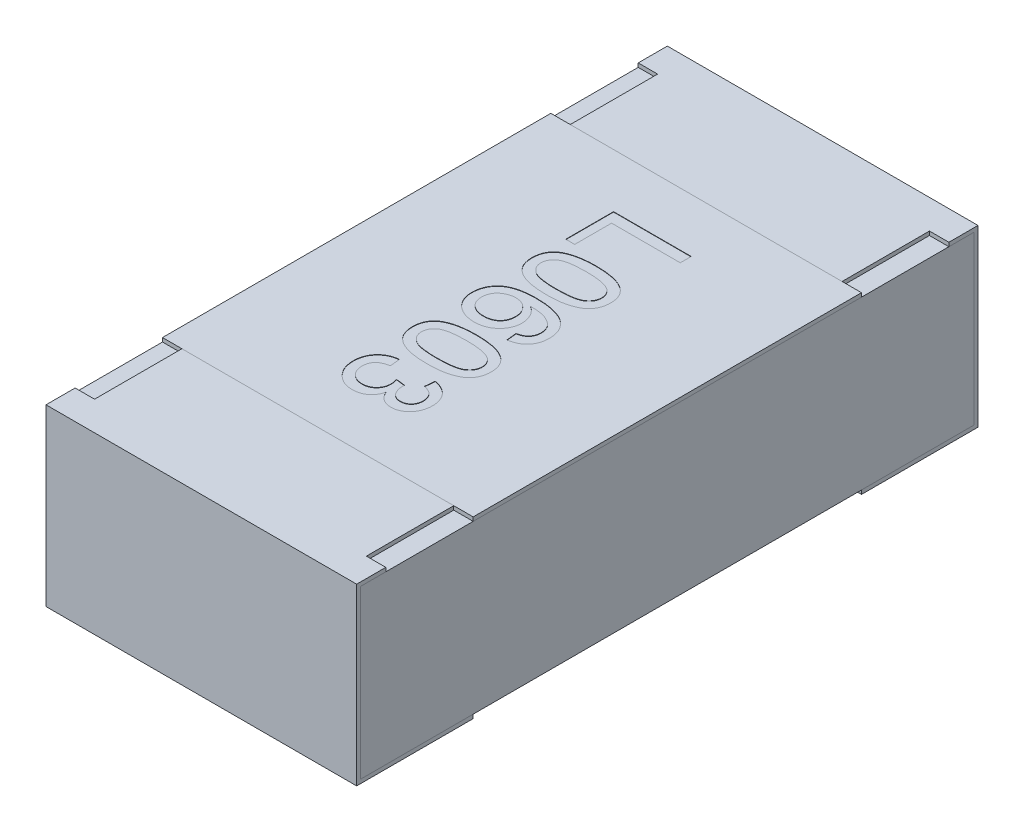
SolidWorks part; units mm, degrees
ref_plane "Front Plane" through (0, 0, 0) normal (0, 0, 1) x (1, 0, 0)
ref_plane "Top Plane" through (0, 0, 0) normal (0, 1, 0) x (1, 0, 0)
ref_plane "Right Plane" through (0, 0, 0) normal (1, 0, 0) x (0, 0, -1)
sketch "Sketch4" plane through (0, 0, 0) normal (1, 0, 0) x (0, 0, -1)
  line L0 (0, 0.1169) -> (0, -0.0721) construction
  line L1 (-0.8, 0) -> (0.3788, 0) construction
  line L2 (-0.8, 0.225) -> (-0.8, -0.225)
  line L3 (-0.8, -0.225) -> (-0.5, -0.225)
  line L4 (-0.5, 0.225) -> (-0.5, 0.215)
  line L5 (-0.5, 0.215) -> (-0.79, 0.215)
  line L6 (-0.79, 0.215) -> (-0.79, -0.215)
  line L7 (-0.79, -0.215) -> (-0.5, -0.215)
  line L8 (-0.5, -0.215) -> (-0.5, -0.225)
  line L9 (-0.5, 0.225) -> (-0.8, 0.225)
  line L10 (0.5, 0.225) -> (0.8, 0.225)
  line L11 (0.5, -0.215) -> (0.5, -0.225)
  line L12 (0.79, -0.215) -> (0.5, -0.215)
  line L13 (0.79, 0.215) -> (0.79, -0.215)
  line L14 (0.5, 0.215) -> (0.79, 0.215)
  line L15 (0.5, 0.225) -> (0.5, 0.215)
  line L16 (0.8, -0.225) -> (0.5, -0.225)
  line L17 (0.8, 0.225) -> (0.8, -0.225)
  dimension "LENGTH" = 0.8
  dimension "HEIGHT" = 0.45
  dimension "END CAP TOP LENGTH" = 0.3
  dimension "END CAP BOTTOM LENGTH" = 0.3
  dimension "D5" = 0.01
  dimension "D6" = 0.01
extrude "Boss-Extrude2" add sketch "Sketch4" along normal mid plane 0.8
sketch "Sketch5" plane through (0, 0, 0) normal (1, 0, 0) x (0, 0, -1)
  line L1 (-0.79, 0.215) -> (0.79, 0.215)
  line L2 (-0.79, 0.215) -> (-0.79, -0.215)
  line L3 (-0.79, -0.215) -> (0.79, -0.215)
  line L4 (0.79, 0.215) -> (0.79, -0.215)
extrude "Boss-Extrude3" add sketch "Sketch5" along normal up to surface and the other way up to surface separate body
sketch "Sketch6" plane through (0, 0.225, 0) normal (0, 1, 0) x (1, 0, 0)
  line L0 (-0.4, 0.8) -> (-0.4, 0.5) construction
  line L1 (-0.4, 0.725) -> (-0.35, 0.725)
  line L2 (-0.4, 0.725) -> (-0.4, 0.5)
  line L3 (-0.4, 0.5) -> (-0.35, 0.5)
  line L4 (-0.35, 0.725) -> (-0.35, 0.5)
  line L5 (0.4, 0.5) -> (-0.4, 0.5) construction
  line L6 (0, 0.0345) -> (0, -0.0345) construction
  line L7 (-0.0325, 0) -> (0.03, 0) construction
  line L8 (0.4, 0.725) -> (0.4, 0.5)
  line L9 (0.4, 0.5) -> (0.35, 0.5)
  line L10 (0.35, 0.725) -> (0.35, 0.5)
  line L11 (0.4, 0.725) -> (0.35, 0.725)
  line L12 (0.4, -0.725) -> (0.35, -0.725)
  line L13 (0.4, -0.725) -> (0.4, -0.5)
  line L14 (0.4, -0.5) -> (0.35, -0.5)
  line L15 (0.35, -0.725) -> (0.35, -0.5)
  line L16 (-0.4, -0.725) -> (-0.35, -0.725)
  line L17 (-0.4, -0.725) -> (-0.4, -0.5)
  line L18 (-0.4, -0.5) -> (-0.35, -0.5)
  line L19 (-0.35, -0.725) -> (-0.35, -0.5)
  dimension "TOP CUT WIDTH" = 0.05
  dimension "TOP CUT LENGTH" = 0.225
extrude "Cut-Extrude1" cut sketch "Sketch6" against normal up to surface (0.01 mm away) up to face at (0, 0.215, 0)
sketch "Sketch7" plane through (0, 0.215, 0) normal (0, 1, 0) x (1, 0, 0)
  line L1 (-0.4, 0.5) -> (0.4, 0.5)
  line L2 (-0.4, 0.5) -> (-0.4, -0.5)
  line L3 (-0.4, -0.5) -> (0.4, -0.5)
  line L4 (0.4, 0.5) -> (0.4, -0.5)
  line L5 (0.35, -0.5) -> (-0.35, -0.5) construction
  line L6 (0.35, 0.5) -> (-0.35, 0.5) construction
  line L7 (-0.4, -0.79) -> (-0.4, 0.79) construction
  line L8 (0.4, 0.79) -> (0.4, -0.79) construction
extrude "Boss-Extrude4" add sketch "Sketch7" along normal up to surface (0.01 mm away) separate body up to face at (0, 0.225, -0.6875)
sketch "Sketch10" plane through (0, 0.225, 0) normal (0, 1, 0) x (1, 0, 0)
  line L0 (-0.1, 0.425) -> (-0.1, -0.425) construction
  line L1 (0, 0) -> (-0.1, 0) construction
  text T0 "L0603" font "Arial" height 0.2
  dimension "D1" = 0.1
  dimension "D2" = 0.85
extrude "TEXT0603" cut sketch "Sketch10" against normal blind 0.001
